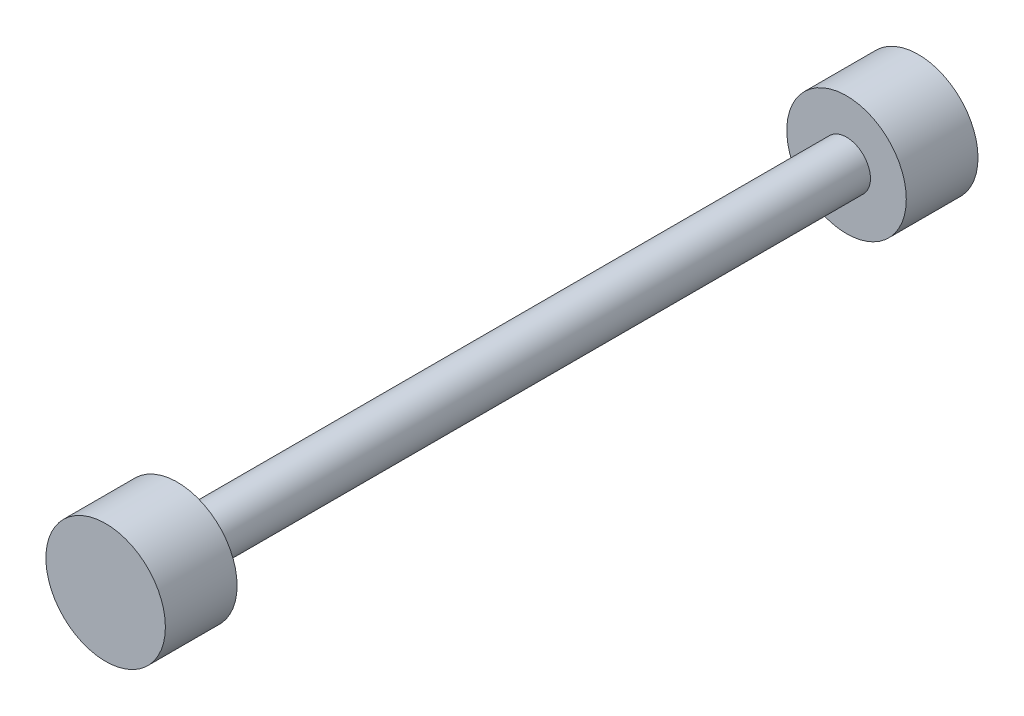
SolidWorks part; units mm, degrees
ref_plane "Front Plane" through (0, 0, 0) normal (0, 0, 1) x (1, 0, 0)
ref_plane "Top Plane" through (0, 0, 0) normal (0, 1, 0) x (1, 0, 0)
ref_plane "Right Plane" through (0, 0, 0) normal (1, 0, 0) x (0, 0, -1)
sketch "Sketch1" plane through (0, 0, 0) normal (0, 0, 1) x (1, 0, 0)
  circle A0 centre (0, 0) radius 15.875
  dimension "D1" = 31.75
extrude "Boss-Extrude1" add sketch "Sketch1" along normal blind 19.05
sketch "Sketch2" plane through (0, 0, 19.05) normal (0, 0, 1) x (1, 0, 0)
  circle A0 centre (0, 0) radius 6.35
  dimension "D1" = 12.7
extrude "Boss-Extrude2" add sketch "Sketch2" along normal blind 177.8
sketch "Sketch3" plane through (0, 0, 196.85) normal (0, 0, 1) x (1, 0, 0)
  circle A0 centre (0, 0) radius 15.875
extrude "Boss-Extrude3" add sketch "Sketch3" along normal blind 19.05
